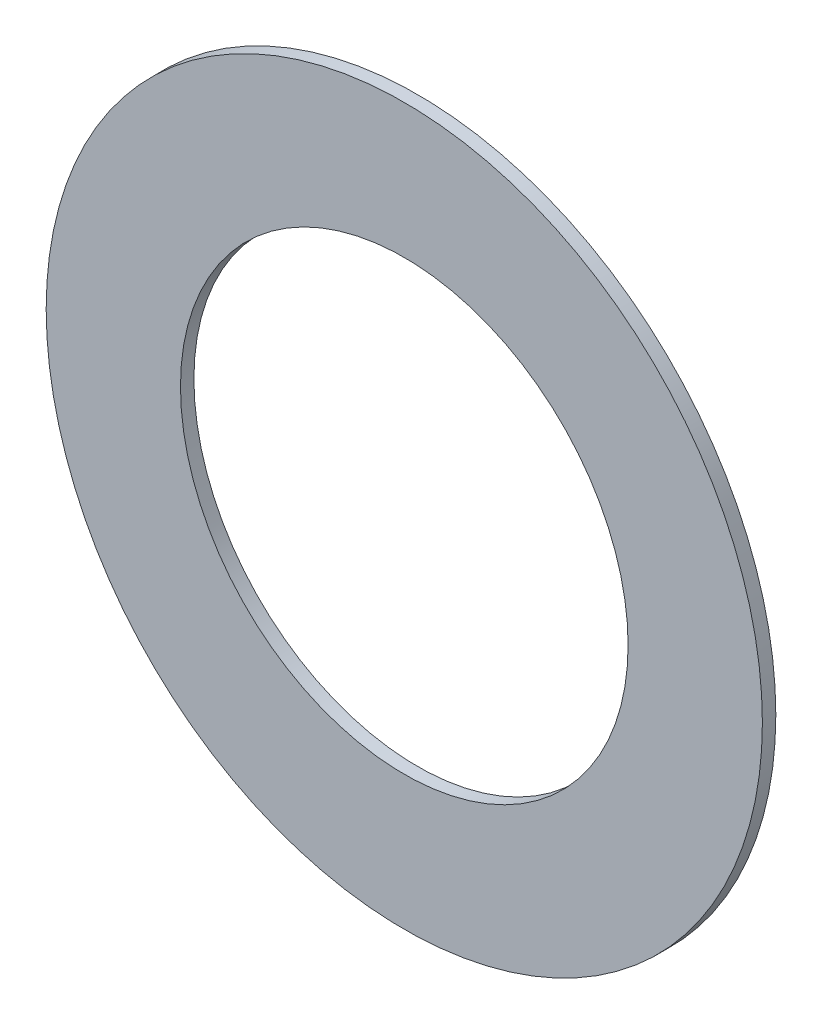
SolidWorks part; units mm, degrees
material "Alloy Steel"
ref_plane "Front Plane" through (0, 0, 0) normal (0, 0, 1) x (1, 0, 0)
ref_plane "Top Plane" through (0, 0, 0) normal (0, 1, 0) x (1, 0, 0)
ref_plane "Right Plane" through (0, 0, 0) normal (1, 0, 0) x (0, 0, -1)
sketch "Sketch1" plane through (0, 0, 0) normal (0, 0, 1) x (1, 0, 0)
  circle A0 centre (0, 0) radius 5
  circle A1 centre (0, 0) radius 8
  dimension "D1" = 16
  dimension "D2" = 10
extrude "Boss-Extrude1" add sketch "Sketch1" along normal blind 0.3
